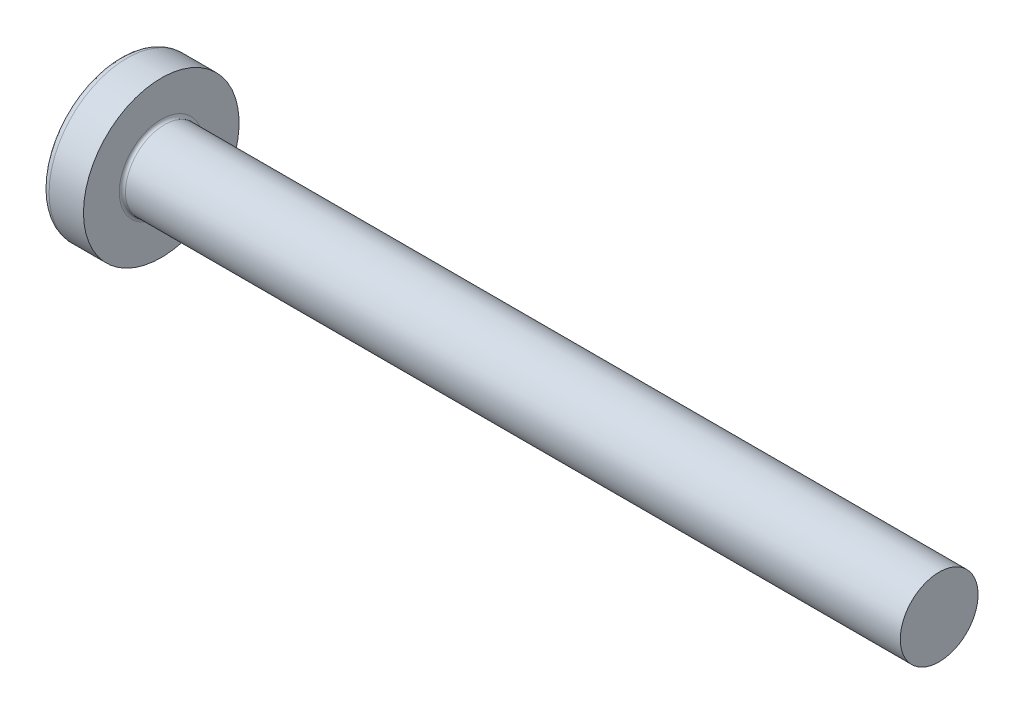
SolidWorks part; units mm, degrees
ref_plane "Plane1" through (0, 0, 0) normal (0, 0, 1) x (1, 0, 0)
ref_plane "Plane2" through (0, 0, 0) normal (0, 1, 0) x (1, 0, 0)
ref_plane "Plane3" through (0, 0, 0) normal (1, 0, 0) x (0, 0, -1)
sketch "BodySke" plane through (0, 0, 0) normal (0, 0, 1) x (1, 0, 0)
  line L0 (2.1, 1.25) -> (2.1, 2.5)
  line L1 (2.325, 6.35) -> (2.325, -3.175) construction
  line L2 (-25.4, 0) -> (127, 0) construction
  line L3 (27.1, 0) -> (0, 0)
  line L4 (2.1, 1.25) -> (27.1, 1.25)
  line L5 (27.1, 1.25) -> (27.1, 0)
  line L6 (0.995, 2.5) -> (2.1, 2.5)
  line L8 (2.1, 6.35) -> (2.1, -3.175) construction
  arc A0 (0.8032, 2.4043) -> (0, 0) centre (4, 0) ccw
  arc A2 (0.8032, 2.4043) -> (0.995, 2.5) centre (0.995, 2.26) cw
  dimension "Head_crown_rad" = 4
  dimension "Head_fillet_rad" = 0.24
  dimension "Length" = 25
  dimension "Head_ht" = 2.1
  dimension "Head_dia" = 5
  dimension "Advance" = 0.45
  dimension "Thread_nom" = 25
  dimension "Diameter" = 2.5
revolve "Base-Revolve" add sketch "BodySke"
cosmetic thread "ThreadCosmetic" [suppressed]
fillet "Fillet1" radius 0.1 1 edges at (2.1, 0, 1.25)
sketch "Sketch3" plane through (0, 0, 0) normal (1, 0, 0) x (0, 0, -1)
  line L0 (0.37, -1.3) -> (-0.37, -1.3)
  line L1 (0.37, -1.3) -> (0.37, 1.3)
  line L2 (-0.37, 1.3) -> (0.37, 1.3)
  line L3 (-0.37, 1.3) -> (-0.37, -1.3)
  dimension "Cross_dia" = 2.6
  dimension "D1" = 1.3
  dimension "Cross_width" = 0.74
  dimension "D2" = 0.37
ref_plane "Plane4" through (1.5, 0, 0) normal (1, 0, 0) x (0, 0, -1)
sketch "Sketch4" plane through (1.5, 0, 0) normal (1, 0, 0) x (0, 0, -1)
  line L0 (0.37, -0.5521) -> (-0.37, -0.5521)
  line L1 (0.37, -0.5521) -> (0.37, 0.5521)
  line L2 (-0.37, 0.5521) -> (0.37, 0.5521)
  line L3 (-0.37, 0.5521) -> (-0.37, -0.5521)
  dimension "D1" = 0.74
  dimension "D2" = 1.1043
  dimension "D3" = 0.37
  dimension "D4" = 0.5521
loft "Recess" cut profiles "Sketch3", "Sketch4"
pattern_circular "RecPat" count 2 every 90 about axis through (0, 0, 0) along (1, 0, 0) of "Recess"
sketch "RecCorSke" plane through (0, 0, 0) normal (0, 0, 1) x (1, 0, 0)
  line L0 (-3.175, 0) -> (15.875, 0) construction
  line L1 (-25.4, 0) -> (127, 0) construction
  line L2 (0, 0) -> (0, 0.6609)
  line L3 (0, 0.6609) -> (1.5, 0.556)
  line L4 (1.5, 0.556) -> (1.6807, 0)
  line L5 (1.6807, 0) -> (0, 0)
  dimension "Diameter" = 1.112
  dimension "Depth" = 1.5
  dimension "Draft_angle" = 4
  dimension "Bottom_angle" = 18
revolve "RecessCore" cut sketch "RecCorSke" angle 360 about L0
sketch "ThdSchSke" plane through (0, 0, 0) normal (0, 0, 1) x (1, 0, 0)
  line L0 (3, -0.9965) -> (2.8225, -1.25)
  line L1 (3, -0.9965) -> (3.1775, -1.25)
  line L2 (3.1775, -1.25) -> (3.1775, -1.5625)
  line L3 (-3.175, 0) -> (5.1513, 0) construction
  line L5 (3.1775, -1.5625) -> (2.8225, -1.5625)
  line L6 (2.8225, -1.5625) -> (2.8225, -1.25)
  dimension "Diameter" = 2.5
  dimension "SideAngle" = 55
  dimension "VeeAngle" = 70
  dimension "Thread_minor" = 1.993
  dimension "Overcut" = 3.125
  dimension "Start" = 3
revolve "ThreadSchematic" [suppressed] cut sketch "ThdSchSke" angle 360 about L3
pattern_linear "ThdSchPat" [suppressed]
equation "\"D1@Sketch3\" = \"Cross_dia@Sketch3\" / 2"
equation "\"D2@Sketch3\" = \"Cross_width@Sketch3\" / 2"
equation "\"Depth@RecCorSke\" = \"Cross_depth@Plane4\""
equation "\"D1@Sketch4\" = \"Cross_width@Sketch3\""
equation "\"D2@Sketch4\" = \"Cross_dia@Sketch3\" - 2.0 * \"Cross_depth@Plane4\" * tan(26.5  * 0.017453292)"
equation "\"D3@Sketch4\" = \"D1@Sketch4\" / 2"
equation "\"D4@Sketch4\" = \"D2@Sketch4\" / 2"
equation "\"Thread_length@ThreadCosmetic\" = ((sgn( (\"Length@BodySke\" - \"Advance@BodySke\" * 2.0 ) - \"Thread_nom@BodySke\" )-1)*( (\"Length@BodySke\" - \"Advance@BodySke\" * 2.0 ) - \"Thread_nom@BodySke\" ))/-2+ \"Thread_nom@BodySke\""
equation "\"Thread_minor@ThdSchSke\" = \"Thread_minor@ThreadCosmetic\""
equation "\"Diameter@ThdSchSke\" = \"Diameter@BodySke\""
equation "\"Overcut@ThdSchSke\" = \"Diameter@BodySke\" * 1.25"
equation "\"Start@ThdSchSke\" = \"Head_ht@BodySke\" + \"Length@BodySke\" - \"Thread_length@ThreadCosmetic\"  '---Non-countersunk---"
equation "\"Num_threads@ThdSchPat\" = int( \"Thread_length@ThreadCosmetic\" / \"Advance@BodySke\" + 0.999 )  + 1"
equation "\"Advance@ThdSchPat\" = \"Thread_length@ThreadCosmetic\" /  (\"Num_threads@ThdSchPat\" - 1) 'relax it"
